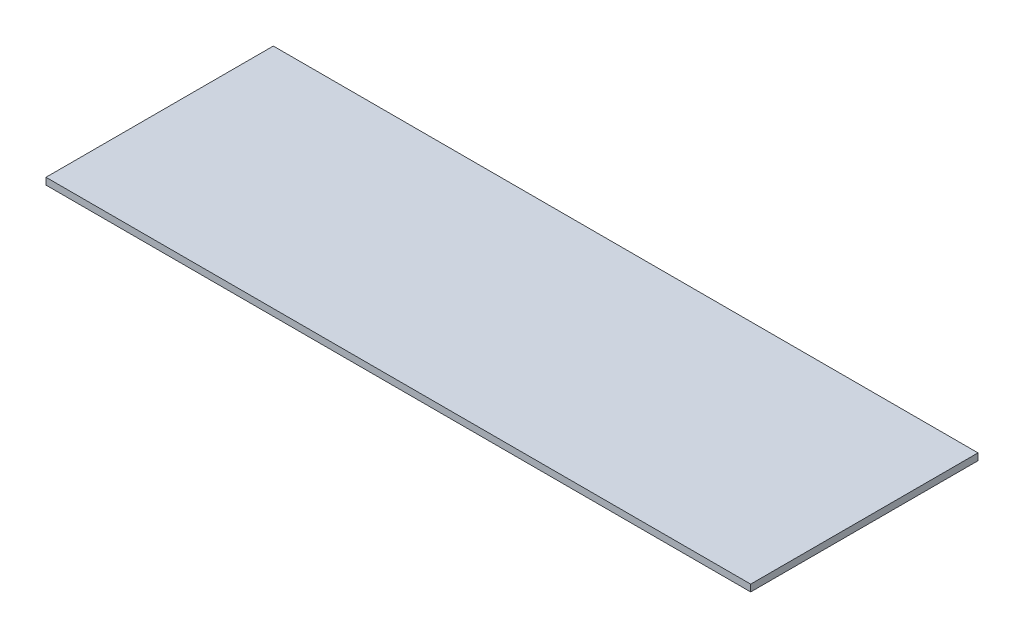
SolidWorks part; units mm, degrees
ref_plane "Front Plane" through (0, 0, 0) normal (0, 0, 1) x (1, 0, 0)
ref_plane "Top Plane" through (0, 0, 0) normal (0, 1, 0) x (1, 0, 0)
ref_plane "Right Plane" through (0, 0, 0) normal (1, 0, 0) x (0, 0, -1)
sketch "Sketch1" plane through (0, 0, 0) normal (0, 1, 0) x (1, 0, 0)
  line L1 (155, -50) -> (-155, -50)
  line L2 (155, -50) -> (155, 50)
  line L3 (155, 50) -> (-155, 50)
  line L4 (-155, -50) -> (-155, 50)
  line L5 (155, -50) -> (-155, 50) construction
  line L6 (155, 50) -> (-155, -50) construction
  point P0 (0, 0)
  dimension "D1" = 310
  dimension "D2" = 100
extrude "Boss-Extrude1" add sketch "Sketch1" along normal blind 3
